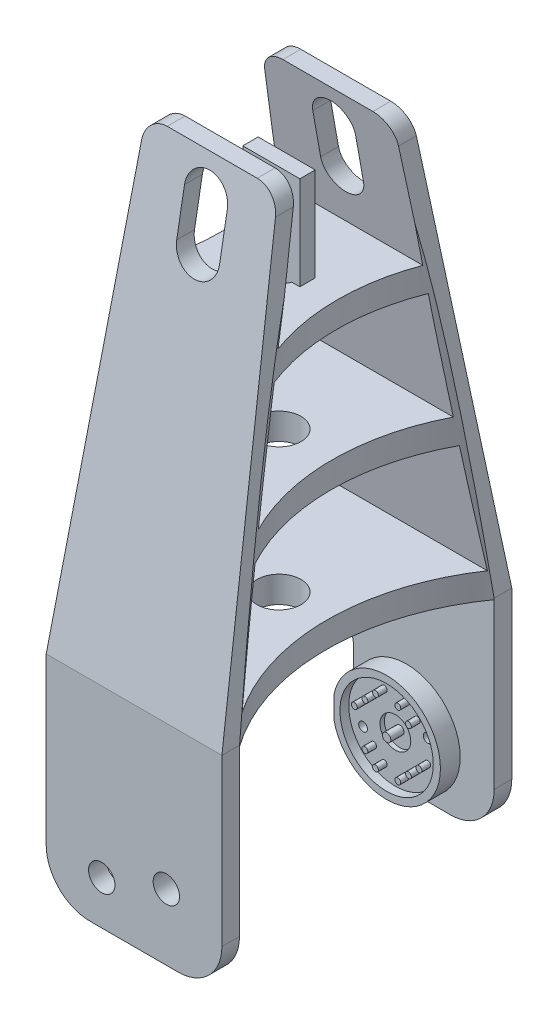
SolidWorks part; units mm, degrees
material "ABS"
ref_plane "Front Plane" through (0, 0, 0) normal (1, 0, 0) x (0, 1, 0)
ref_plane "Top Plane" through (0, 0, 0) normal (0, 0, 1) x (0, 1, 0)
ref_plane "Right Plane" through (0, 0, 0) normal (0, 1, 0) x (-1, 0, 0)
sketch "Sketch1" plane through (0, 0, 0) normal (1, 0, 0) x (0, 1, 0)
  line L1 (-14.7727, -33) -> (35.2273, -33)
  line L2 (-14.7727, -33) -> (-14.7727, -29)
  line L3 (-14.7727, 33) -> (35.2273, 33)
  line L7 (-14.7727, 29) -> (34.9178, 29)
  line L9 (-14.7727, -29) -> (34.9178, -29)
  line L12 (-14.7727, 29) -> (-14.7727, 33)
  line L13 (35.2273, 33) -> (135.2273, 15.1954)
  line L14 (35.2273, -33) -> (135.2273, -15.1954)
  line L34 (40.9178, -27.9239) -> (67.0725, -23.2672)
  line L55 (0, -24.5) -> (0, 49975.5) construction
  line L82 (-1000, 0) -> (49000, 0) construction
  line L89 (135.2273, -15.1954) -> (135.2273, -11.1325)
  line L109 (34.9178, 29) -> (34.9178, -29)
  line L124 (40.9178, 27.9239) -> (40.9178, -27.9239)
  line L125 (37.9178, 30.7499) -> (130.9178, 30.7499) construction
  line L131 (105.2273, 16.4739) -> (135.2273, 11.1325)
  line L132 (37.9178, 48.0003) -> (37.9178, -26.7501) construction
  line L133 (37.9178, 29) -> (37.9178, -29) construction
  line L135 (73.0725, 22.1989) -> (99.2273, 17.5422)
  line L136 (40.9178, 27.9239) -> (67.0725, 23.2672)
  line L137 (73.0725, -22.1989) -> (99.2273, -17.5422)
  line L138 (105.2273, -16.4739) -> (135.2273, -11.1325)
  line L140 (40.9178, 29) -> (40.9178, -29) construction
  line L141 (135.2273, 11.1325) -> (135.2273, 15.1954)
  line L142 (67.0725, 23.2672) -> (67.0725, -23.2672)
  line L143 (40.9178, 3.7794) -> (67.0725, 3.7794) construction
  line L144 (61.4405, 22.5852) -> (61.4405, -26.6334) construction
  line L145 (67.0725, 3.7794) -> (73.0725, 3.7794) construction
  line L146 (73.0725, 22.1989) -> (73.0725, -22.1989)
  line L147 (73.0725, 3.7794) -> (99.2273, 3.7794) construction
  line L148 (99.2273, 17.5422) -> (99.2273, -17.5422)
  line L149 (-14.7727, 29) -> (-14.7727, 0) construction
  line L150 (85.1905, 18.8875) -> (85.1905, -18.8875) construction
  line L151 (-14.7727, 0) -> (-14.7727, -29) construction
  line L152 (105.2273, 16.4739) -> (105.2273, -16.4739)
  line L156 (108.9405, 15.1898) -> (108.9405, -15.1898) construction
  circle A0 centre (135, 0) radius 15 construction
  point P30 (19.6628, -23.2325)
  point P49 (118.934, 0)
  dimension "D18" = 4
  dimension "D15" = 22.265
  dimension "D3" = 30
  dimension "D4" = 4
  dimension "D5" = 135
  dimension "D6" = 58
  dimension "D8" = 50
  dimension "D9" = 6
  dimension "D10" = 6
  dimension "D11" = 93
  dimension "D20" = 30
  dimension "D21" = 26.1548
  dimension "D24" = 6
  dimension "D12" = 3
  dimension "D13" = 4
  dimension "D14" = 4
  dimension "D16" = 49.6905
  dimension "D19" = 4
extrude "Boss-Extrude1" add sketch "Sketch1" along normal mid plane 40
sketch "Sketch6" plane through (0, 0, -29) normal (0, 0, 1) x (1, 0, 0)
  circle A0 centre (0, 0) radius 12.25
  dimension "D1" = 24.5
extrude "Boss-Extrude2" add sketch "Sketch6" along normal blind 4.5
sketch "Sketch4" plane through (0, 0, 0) normal (0, 0, 1) x (0, 1, 0)
  line L1 (-17.5, 25) -> (140.2273, 25)
  line L2 (-17.5, 25) -> (-17.5, -25)
  line L3 (-17.5, -25) -> (140.2273, -25)
  line L4 (140.2273, 25) -> (140.2273, -25)
  line L6 (-12.5, -20) -> (-12.5, 20) construction
  line L10 (-12.5, 0) -> (150, 0) construction
  line L11 (35.2273, 20) -> (130.477, 15.2375)
  line L12 (35.2273, -20) -> (130.477, -15.2375)
  line L14 (-2.5, 20) -> (35.2273, 20)
  line L15 (-12.5, 10) -> (-12.5, -10)
  line L16 (-2.5, -20) -> (35.2273, -20)
  line L65 (35.2273, -1010.7326) -> (35.2273, 48989.2674) construction
  line L69 (135.2273, 10.2438) -> (135.2273, -10.2438)
  line L71 (35.2273, 20) -> (135.2273, 20) construction
  line L72 (35.2273, -20) -> (135.2273, -20) construction
  line L73 (135.2273, -20) -> (135.2273, 20) construction
  arc A3 (-2.5, -20) -> (-12.5, -10) centre (-2.5, -10) cw
  arc A4 (-12.5, 10) -> (-2.5, 20) centre (-2.5, 10) cw
  circle A6 centre (0, 0) radius 2.75 construction
  circle A7 centre (0, 0) radius 3 construction
  arc A8 (130.477, -15.2375) -> (135.2273, -10.2438) centre (130.2273, -10.2438) ccw
  arc A9 (135.2273, 10.2438) -> (130.477, 15.2375) centre (130.2273, 10.2438) ccw
  point P21 (135.2273, -15)
  point P24 (135.2273, 15)
  dimension "D3" = 10
  dimension "D4" = 5
  dimension "D2" = 30
  dimension "D5" = 12.5
  dimension "D10" = 6
  dimension "D11" = 5
  dimension "D9" = 5.5
  dimension "D6" = 5
  dimension "D7" = 5
  dimension "D8" = 5
  dimension "D12" = 40
extrude "Cut-Extrude10" cut sketch "Sketch4" along normal mid plane 69.2813
sketch "Sketch8" plane through (0, 0, 0) normal (0, 0, 1) x (0, 1, 0)
  line L0 (-1000, 0) -> (49000, 0) construction
  line L1 (117.1273, 0) -> (127.1273, 0) construction
  line L2 (117.1273, 4.875) -> (127.1273, 4.875)
  line L3 (117.1273, -4.875) -> (127.1273, -4.875)
  line L5 (135.2273, -15) -> (135.2273, 15) construction
  arc A0 (117.1273, 4.875) -> (117.1273, -4.875) centre (117.1273, 0) ccw
  arc A1 (127.1273, -4.875) -> (127.1273, 4.875) centre (127.1273, 0) ccw
  point P5 (122.1273, 0)
  dimension "D2" = 4.875
  dimension "D1" = 8.1
  dimension "D3" = 10
extrude "Cut-Extrude12" cut sketch "Sketch8" against normal through all and the other way through all
sketch "Sketch11" plane through (0, 0, -24.5) normal (0, 0, 1) x (1, 0, 0)
  line L0 (-1000, 0) -> (49000, 0) construction
  line L1 (0, -1000) -> (0, 49000) construction
  line L2 (0, 0) -> (35355.3391, 35355.3391) construction
  line L5 (7.3539, 2.5456) -> (2.5456, 7.3539) construction
  circle A1 centre (0, 0) radius 0.95
  circle A2 centre (0, 0) radius 10.625
  circle A6 centre (2.5456, 7.3539) radius 0.675
  circle A7 centre (4.9497, 4.9497) radius 0.675
  circle A8 centre (7.3539, 2.5456) radius 0.675 construction
  circle A9 centre (-2.5456, 7.3539) radius 0.675
  circle A10 centre (-4.9497, 4.9497) radius 0.675
  circle A11 centre (-7.3539, 2.5456) radius 0.675
  circle A12 centre (-7.3539, -2.5456) radius 0.675 construction
  circle A13 centre (-4.9497, -4.9497) radius 0.675
  circle A14 centre (-2.5456, -7.3539) radius 0.675
  circle A15 centre (7.3539, -2.5456) radius 0.675
  circle A16 centre (2.5456, -7.3539) radius 0.675
  circle A17 centre (4.9497, -4.9497) radius 0.675
  dimension "D1" = 21.25
  dimension "D4" = 1.35
  dimension "D6" = 5.0912
  dimension "D8" = 1.9
  dimension "D2" = 45
  dimension "D3" = 7
  dimension "D5" = 3.4
  dimension "D7" = 3.4
extrude "Cut-Extrude13" cut sketch "Sketch11" against normal blind 2
sketch "Sketch12" plane through (0, 0, -26.5) normal (0, 0, 1) x (1, 0, 0)
  circle A0 centre (0, 0) radius 3.5
  circle A1 centre (0, 0) radius 0.95
  circle A2 centre (0, 0) radius 0.95 construction
  dimension "D1" = 7
extrude "Cut-Extrude14" cut sketch "Sketch12" against normal blind 1
sketch "Sketch13" plane through (0, 0, -33) normal (0, 0, -1) x (1, 0, 0)
  line L0 (10, 12.5) -> (-10, 12.5) construction
  line L1 (-9, 12.5) -> (-20, 12.5)
  line L2 (-12, 9.5) -> (-12, -9.5)
  line L4 (-20, 12.5) -> (-20, -21.5)
  line L5 (-20, 2.5) -> (-20, -35.2273) construction
  arc A0 (-16.9231, -16.8846) -> (-12, -9.5) centre (-20, -9.5) ccw
  arc A1 (-16.9231, -16.8846) -> (-20, -21.5) centre (-15, -21.5) ccw
  arc A2 (-9, 12.5) -> (-12, 9.5) centre (-9, 9.5) ccw
  dimension "D2" = 11
  dimension "D3" = 5
  dimension "D4" = 3
  dimension "D5" = 8
  dimension "D1" = 19
extrude "Cut-Extrude15" cut sketch "Sketch13" against normal up to next
sketch "Sketch14" plane through (0, 105.2273, 0) normal (0, 1, 0) x (-1, 0, 0)
  line L3 (-1000, 0) -> (49000, 0) construction
  line L4 (0, -1000) -> (0, 49000) construction
  circle A4 centre (0, 0) radius 5
  dimension "D1" = 10
extrude "Cut-Extrude16" cut sketch "Sketch14" against normal through all
sketch "Sketch15" plane through (0, 34.9178, 0) normal (0, -1, 0) x (1, 0, 0)
  line L0 (-22.5023, 32.227) -> (-22.5023, -32.227)
  line L1 (0, -1000) -> (0, 49000) construction
  line L2 (22.5023, 32.227) -> (22.5023, -32.227)
  arc A0 (-22.5023, -32.227) -> (-22.5023, 32.227) centre (-60.7308, 0) ccw
  arc A1 (22.5023, -32.227) -> (22.5023, 32.227) centre (60.7308, 0) cw
  dimension "D1" = 100
extrude "Cut-Extrude17" cut sketch "Sketch15" against normal through all draft 2.1
sketch "Sketch16" plane through (0, 0, -26.5) normal (0, 0, 1) x (1, 0, 0)
  line L0 (2.5456, 7.3539) -> (7.3539, 2.5456) construction
  line L1 (-1000, 0) -> (49000, 0) construction
  line L2 (0, -1000) -> (0, 49000) construction
  line L3 (0, 0) -> (35355.3391, 35355.3391) construction
  line L4 (0, 0) -> (-35355.3391, 35355.3391) construction
  circle A0 centre (4.9497, 4.9497) radius 0.675 construction
  circle A2 centre (2.5456, 7.3539) radius 1 construction
  circle A4 centre (-7.3539, -2.5456) radius 1
  circle A5 centre (7.3539, 2.5456) radius 1
  circle A6 centre (2.5456, -7.3539) radius 1 construction
  circle A7 centre (4.9497, -4.9497) radius 0.675 construction
  circle A9 centre (4.9497, 4.9497) radius 0.675 construction
  dimension "D1" = 2
extrude "Cut-Extrude18" cut sketch "Sketch16" against normal up to next
sketch "Sketch18" plane through (0, 0, 29) normal (0, 0, -1) x (1, 0, 0)
  circle A0 centre (0, 0) radius 6.25
  dimension "D1" = 12.5
extrude "Boss-Extrude4" add sketch "Sketch18" along normal blind 5.5 and the other way up to surface (4 mm away) other way up to face at (0, 6.0521, 33)
sketch "Sketch19" plane through (0, 105.2273, 0) normal (0, 1, 0) x (-1, 0, 0)
  line L0 (-1000, 0) -> (49000, 0) construction
  line L1 (0, -1000) -> (0, 49000) construction
  line L3 (-6.5, -1.75) -> (6.5, -1.75)
  line L4 (-6.5, -1.75) -> (-6.5, 1.75)
  line L5 (-6.5, 1.75) -> (6.5, 1.75)
  line L6 (6.5, -1.75) -> (6.5, 1.75)
  line L7 (0, 1.75) -> (0, -1.75) construction
  line L8 (-6.5, 0) -> (6.5, 0) construction
  point P4 (0, 0)
  dimension "D1" = 3.5
  dimension "D2" = 13
extrude "Boss-Extrude5" add sketch "Sketch19" along normal blind 21.3 and the other way up to surface other way up to face at (0, 99.2273, 5)
sketch "Sketch20" plane through (0, 0, 23.5) normal (0, 0, -1) x (1, 0, 0)
  circle A0 centre (0, 0) radius 7.5
  dimension "D1" = 15
extrude "Boss-Extrude6" add sketch "Sketch20" against normal blind 0.75
sketch "Sketch17" plane through (0, 0, 33) normal (0, 0, 1) x (1, 0, 0)
  line L3 (-1000, 0) -> (49000, 0) construction
  line L4 (0, -1000) -> (0, 49000) construction
  circle A9 centre (7.3539, 2.5456) radius 1 construction
  circle A10 centre (7.3539, 2.5456) radius 1 construction
  circle A15 centre (7.3539, 2.5456) radius 3
  circle A16 centre (-7.3539, -2.5456) radius 3
  circle A17 centre (-7.3539, -2.5456) radius 1 construction
  dimension "D1" = 6
extrude "Cut-Extrude19" cut sketch "Sketch17" against normal up to next
